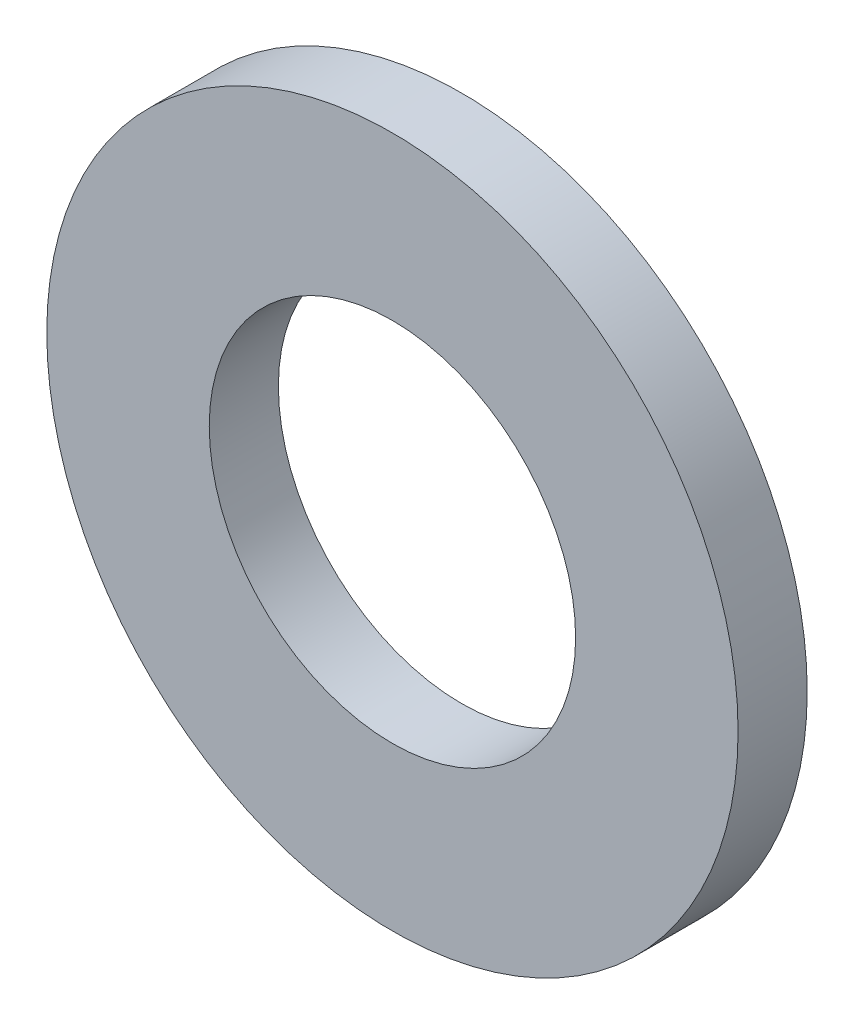
SolidWorks part; units mm, degrees
material "Plain Carbon Steel"
ref_plane "Front Plane" through (0, 0, 0) normal (0, 0, 1) x (1, 0, 0)
ref_plane "Top Plane" through (0, 0, 0) normal (0, 1, 0) x (1, 0, 0)
ref_plane "Right Plane" through (0, 0, 0) normal (1, 0, 0) x (0, 0, -1)
sketch "Sketch1" plane through (0, 0, 0) normal (0, 0, 1) x (1, 0, 0)
  circle A0 centre (0, 0) radius 2.65
  circle A1 centre (0, 0) radius 5
  dimension "ID" = 5.3
  dimension "OD" = 10
extrude "Extrude1" add sketch "Sketch1" against normal blind 1
